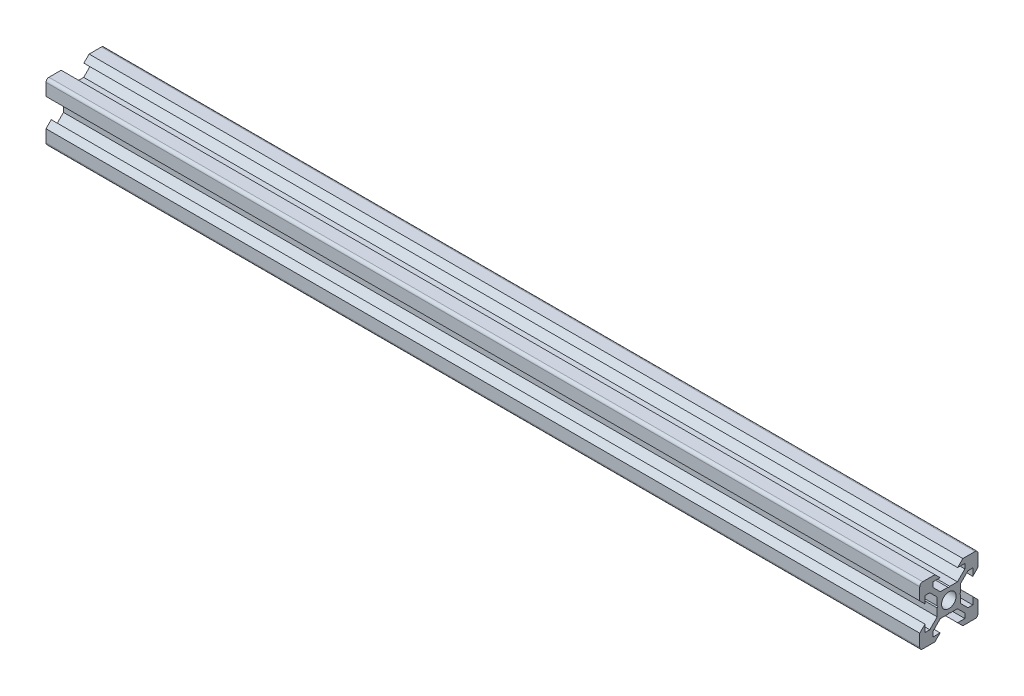
SolidWorks part; units mm, degrees
material "6063-T5"
material "6063-T5"
ref_plane "Plano frontal" through (0, 0, 0) normal (0, 0, 1) x (1, 0, 0)
ref_plane "Plano superior" through (0, 0, 0) normal (0, 1, 0) x (1, 0, 0)
ref_plane "Plano direito" through (0, 0, 0) normal (1, 0, 0) x (0, 0, -1)
sketch "Esboço1" plane through (0, 0, 0) normal (0, 0, 1) x (1, 0, 0)
  line L0 (0, 0) -> (300, 0)
  dimension "D1" = 300
other "Quadrado PF20-11 - PERFIL 2020 V-SLOT(1)"
ref_plane "Plano1" through (0, 0, 0) normal (1, 0, 0) x (0, 1, 0)
sketch "Sketch11" plane through (0, 0, 0) normal (1, 0, 0) x (0, 1, 0)
  line L0 (-4.8, 10) -> (-3, 8.2)
  line L1 (-3, 8.2) -> (-5.5, 8.2)
  line L2 (-5.5, 8.2) -> (-5.5, 6.5607)
  line L3 (-5.5, 6.5607) -> (-2.9393, 4)
  line L4 (-2.9393, 4) -> (-0.3, 4)
  line L5 (5.5, 6.5607) -> (2.9393, 4)
  line L6 (5.5, 8.2) -> (5.5, 6.5607)
  line L7 (3, 8.2) -> (5.5, 8.2)
  line L8 (4.8, 10) -> (3, 8.2)
  line L9 (-0.3, 4) -> (0, 3.7)
  line L10 (0.3, 4) -> (0, 3.7)
  line L11 (0.3, 4) -> (2.9393, 4)
  line L12 (9, 10) -> (4.8, 10)
  line L13 (10, 4.8) -> (8.2, 3)
  line L14 (10, 4.8) -> (10, 9)
  line L15 (8.2, 3) -> (8.2, 5.5)
  line L16 (8.2, 5.5) -> (6.5607, 5.5)
  line L17 (6.5607, 5.5) -> (4, 2.9393)
  line L18 (4.8, -10) -> (3, -8.2)
  line L19 (3, -8.2) -> (5.5, -8.2)
  line L20 (5.5, -8.2) -> (5.5, -6.5607)
  line L21 (5.5, -6.5607) -> (2.9393, -4)
  line L22 (2.9393, -4) -> (0.3, -4)
  line L23 (0.3, -4) -> (0, -3.7)
  line L24 (-0.3, -4) -> (0, -3.7)
  line L25 (-0.3, -4) -> (-2.9393, -4)
  line L26 (-5.5, -6.5607) -> (-2.9393, -4)
  line L27 (-5.5, -8.2) -> (-5.5, -6.5607)
  line L28 (-3, -8.2) -> (-5.5, -8.2)
  line L29 (-4.8, -10) -> (-3, -8.2)
  line L30 (-10, -4.8) -> (-10, -9)
  line L31 (-10, -4.8) -> (-8.2, -3)
  line L32 (-8.2, -3) -> (-8.2, -5.5)
  line L33 (-8.2, -5.5) -> (-6.5607, -5.5)
  line L34 (-6.5607, -5.5) -> (-4, -2.9393)
  line L35 (-4, -2.9393) -> (-4, -0.3)
  line L36 (-4, -0.3) -> (-3.7, 0)
  line L37 (-4, 0.3) -> (-3.7, 0)
  line L38 (-4, 0.3) -> (-4, 2.9393)
  line L39 (-6.5607, 5.5) -> (-4, 2.9393)
  line L40 (-8.2, 5.5) -> (-6.5607, 5.5)
  line L41 (-8.2, 3) -> (-8.2, 5.5)
  line L42 (-10, 4.8) -> (-8.2, 3)
  line L43 (-4.8, 10) -> (-9, 10)
  line L44 (4, 2.9393) -> (4, 0.3)
  line L45 (4, 0.3) -> (3.7, 0)
  line L46 (4, -0.3) -> (3.7, 0)
  line L47 (4, -0.3) -> (4, -2.9393)
  line L48 (6.5607, -5.5) -> (4, -2.9393)
  line L49 (8.2, -5.5) -> (6.5607, -5.5)
  line L50 (8.2, -3) -> (8.2, -5.5)
  line L51 (10, -4.8) -> (8.2, -3)
  line L52 (10, -9) -> (10, -4.8)
  line L53 (4.8, -10) -> (9, -10)
  line L106 (-10, 9) -> (-10, 4.8)
  line L107 (-9, -10) -> (-4.8, -10)
  arc A0 (10, 9) -> (9, 10) centre (9, 9) ccw
  arc A1 (9, -10) -> (10, -9) centre (9, -9) ccw
  arc A3 (-10, -9) -> (-9, -10) centre (-9, -9) ccw
  arc A4 (-9, 10) -> (-10, 9) centre (-9, 9) ccw
  circle A7 centre (0, 0) radius 2.5
  point P1 (-10, 10)
  point P3 (10, 10)
  point P4 (10, -10)
  point P68 (0, 0)
  point P70 (10, 0)
  point P71 (0, 0)
  point P72 (0, 0)
  point P113 (0, -10)
  point P114 (-10, -10)
  point P115 (-10, 0)
  point P116 (0, 10)
  point P118 (0, 0)
